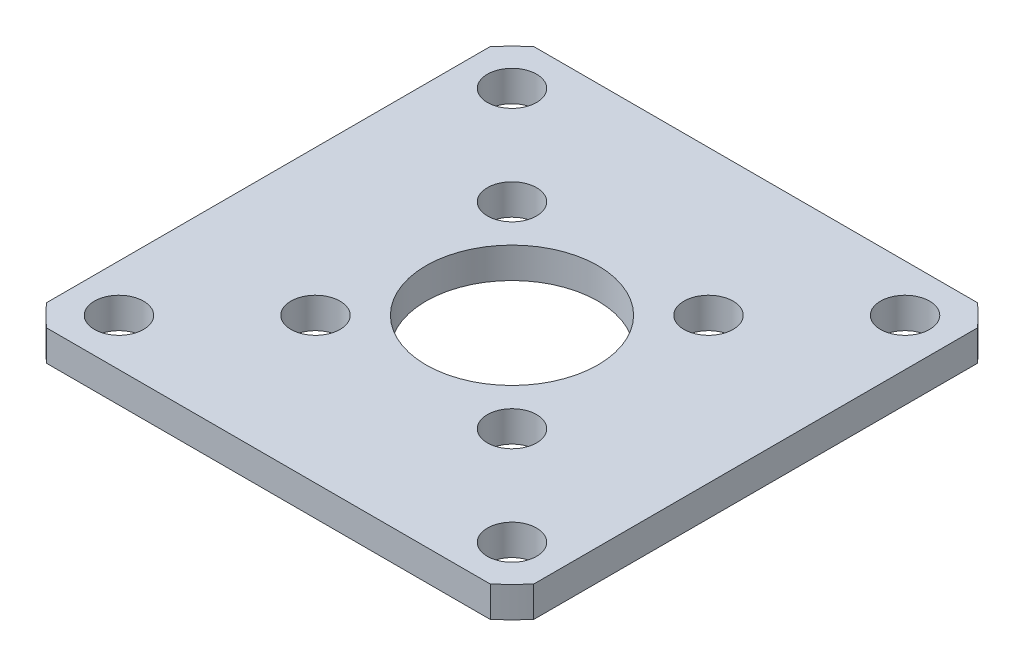
SolidWorks part; units mm, degrees
ref_plane "Front Plane" through (0, 0, 0) normal (0, 0, 1) x (1, 0, 0)
ref_plane "Top Plane" through (0, 0, 0) normal (0, 1, 0) x (1, 0, 0)
ref_plane "Right Plane" through (0, 0, 0) normal (1, 0, 0) x (0, 0, -1)
sketch "Sketch1" plane through (0, 0, 0) normal (0, 1, 0) x (1, 0, 0)
  line L0 (0, 0) -> (-16, 16)
  line L2 (0, 0) -> (-16, 0)
  line L3 (0, 0) -> (0, 16)
  line L4 (0, 16) -> (-16, 16)
  line L5 (-16, 0) -> (-16, 16)
  line L6 (16, -16) -> (-16, -16)
  line L7 (16, -16) -> (16, 16)
  line L8 (16, 16) -> (-16, 16)
  line L9 (-16, -16) -> (-16, 16)
  line L10 (16, -16) -> (-16, 16) construction
  line L11 (16, 16) -> (-16, -16) construction
  circle A0 centre (0, 0) radius 7
  circle A1 centre (-16, 16) radius 2
  circle A2 centre (16, 16) radius 2
  circle A3 centre (16, -16) radius 2
  circle A4 centre (-16, -16) radius 2
  circle A5 centre (0, 0) radius 26.83
extrude "Boss-Extrude1" add sketch "Sketch1" along normal blind 2.5 contours A1 L5 L2 A0 L0 | A5 A4 L9 L5 A1 L4 L8 A2 L7 A3 L6 | A4 L6 A3 L7 A2 L8 L3 A0 L2 L9 | A1 L0 A0 L3 L4
sketch "Sketch2" plane through (0, 2.5, 0) normal (0, 1, 0) x (1, 0, 0)
  line L0 (0, 0) -> (-8, -8)
  line L2 (8, 8) -> (-8, 8)
  line L3 (8, 8) -> (8, -8)
  line L4 (8, -8) -> (-8, -8)
  line L5 (-8, 8) -> (-8, -8)
  line L6 (8, 8) -> (-8, -8) construction
  line L7 (8, -8) -> (-8, 8) construction
  circle A0 centre (-8, 8) radius 2
  circle A1 centre (8, 8) radius 2
  circle A2 centre (8, -8) radius 2
  circle A3 centre (-8, -8) radius 2
extrude "Cut-Extrude1" cut sketch "Sketch2" against normal blind 10 contours L2 A0 L5 | L5 A0 L2 | L3 A1 L2 | L2 A1 L3 | L5 A3 L4 | L4 A3 L0 | L0 A3 L5 | L4 A2 L3 | L3 A2 L4
sketch "Sketch3" plane through (0, 2.5, 0) normal (0, 1, 0) x (1, 0, 0)
  line L0 (0, 0) -> (16, 16)
  line L1 (16, 16) -> (19.8339, 19.8339)
  line L3 (-19.8339, -19.8339) -> (19.8339, -19.8339)
  line L4 (-19.8339, -19.8339) -> (-19.8339, 19.8339)
  line L5 (-19.8339, 19.8339) -> (19.8339, 19.8339)
  line L6 (19.8339, -19.8339) -> (19.8339, 19.8339)
  line L7 (-19.8339, -19.8339) -> (19.8339, 19.8339) construction
  line L8 (-19.8339, 19.8339) -> (19.8339, -19.8339) construction
  circle M10 centre (0, 0) radius 26.83
extrude "Cut-Extrude2" cut sketch "Sketch3" against normal blind 10 contours L4 M10 | L5 M10 | L6 M10 | L3 M10
